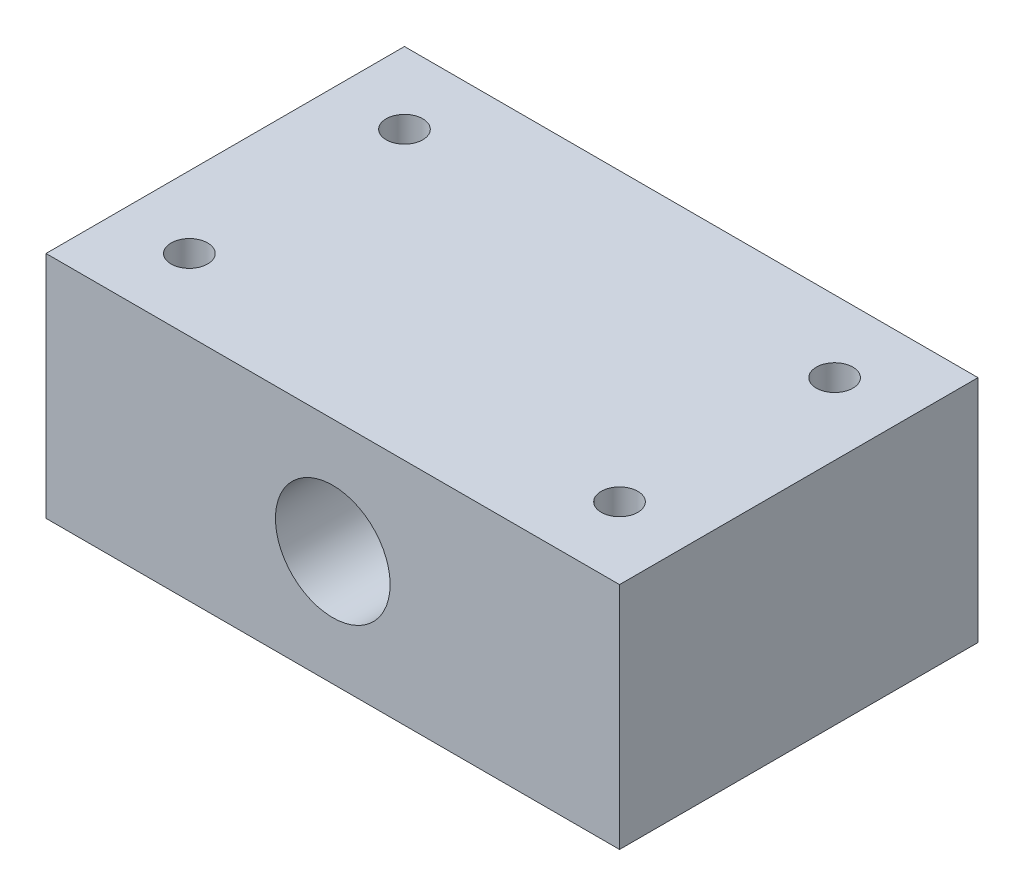
SolidWorks part; units mm, degrees
ref_plane "Front Plane" through (0, 0, 0) normal (0, 0, 1) x (1, 0, 0)
ref_plane "Top Plane" through (0, 0, 0) normal (0, 1, 0) x (1, 0, 0)
ref_plane "Right Plane" through (0, 0, 0) normal (1, 0, 0) x (0, 0, -1)
sketch "Sketch1" plane through (0, 0, 0) normal (0, 1, 0) x (1, 0, 0)
  line L0 (0, 25) -> (0, -25) construction
  line L1 (-40, 25) -> (40, 25)
  line L2 (-40, 25) -> (-40, -25)
  line L3 (-40, -25) -> (40, -25)
  line L4 (40, 25) -> (40, -25)
  line L5 (-40, 25) -> (40, -25) construction
  line L6 (-40, -25) -> (40, 25) construction
  line L7 (-40, 0) -> (40, 0) construction
  circle A0 centre (-30, 15) radius 2.55
  circle A1 centre (30, 15) radius 2.55
  circle A2 centre (30, -15) radius 2.55
  circle A3 centre (-30, -15) radius 2.55
  point P0 (0, 0)
  dimension "D3" = 5.1
  dimension "D1" = 80
  dimension "D2" = 50
  dimension "D4" = 60
  dimension "D5" = 30
extrude "Boss-Extrude1" add sketch "Sketch1" along normal blind 32
sketch "Sketch2" plane through (0, 0, 25) normal (0, 0, 1) x (1, 0, 0)
  line L0 (0, 32) -> (0, 0) construction
  line L2 (-40, 32) -> (40, 32) construction
  circle A0 centre (0, 16) radius 8
extrude "Cut-Extrude1" cut sketch "Sketch2" against normal blind 50 contours A0
